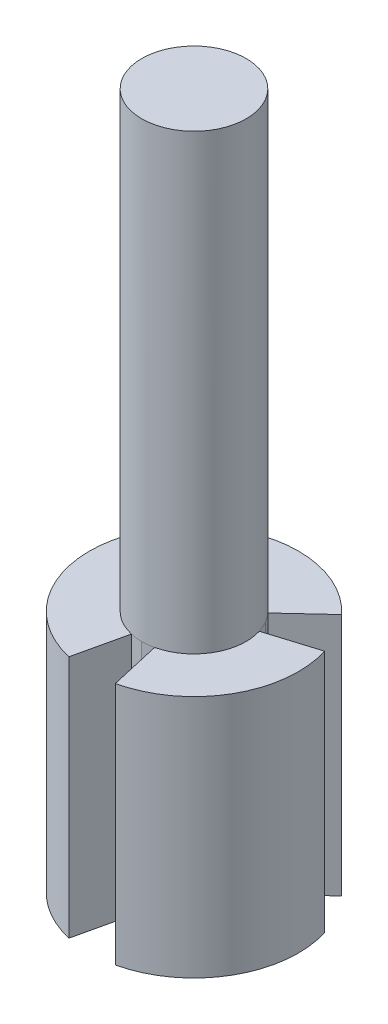
SolidWorks part; units mm, degrees
material "Plain Carbon Steel"
ref_plane "Front Plane" through (0, 0, 0) normal (0, 0, 1) x (1, 0, 0)
ref_plane "Top Plane" through (0, 0, 0) normal (0, 1, 0) x (1, 0, 0)
ref_plane "Right Plane" through (0, 0, 0) normal (1, 0, 0) x (0, 0, -1)
sketch "Sketch1" plane through (0, 0, 0) normal (0, 1, 0) x (1, 0, 0)
  circle A0 centre (0, 0) radius 15
  dimension "D1" = 30
extrude "Boss-Extrude1" add sketch "Sketch1" along normal blind 200
sketch "Sketch2" plane through (0, 0, 0) normal (0, -1, 0) x (1, 0, 0)
  circle A0 centre (0, 0) radius 30
  circle A1 centre (0, 0) radius 15 construction
  circle A2 centre (0, 0) radius 15
  dimension "D1" = 60
extrude "Boss-Extrude2" add sketch "Sketch2" against normal blind 70
sketch "Sketch3" plane through (0, 70, 0) normal (0, 1, 0) x (1, 0, 0)
  line L0 (-3.3336, -14.6249) -> (-7.4154, -32.5319)
  line L1 (-3.3336, -14.6249) -> (0, -15)
  line L2 (0, -15) -> (3.3336, -14.6249)
  line L3 (3.3336, -14.6249) -> (7.4154, -32.5319)
  line L4 (-7.4154, -32.5319) -> (7.4154, -32.5319)
  circle A1 centre (0, 0) radius 15 construction
  circle A2 centre (0, 0) radius 15 construction
extrude "Cut-Extrude1" cut sketch "Sketch3" against normal blind 84
pattern_circular "CirPattern2" count 3 every 120 about axis through (0, 0, 0) along (0, 1, 0) of "Cut-Extrude1"
